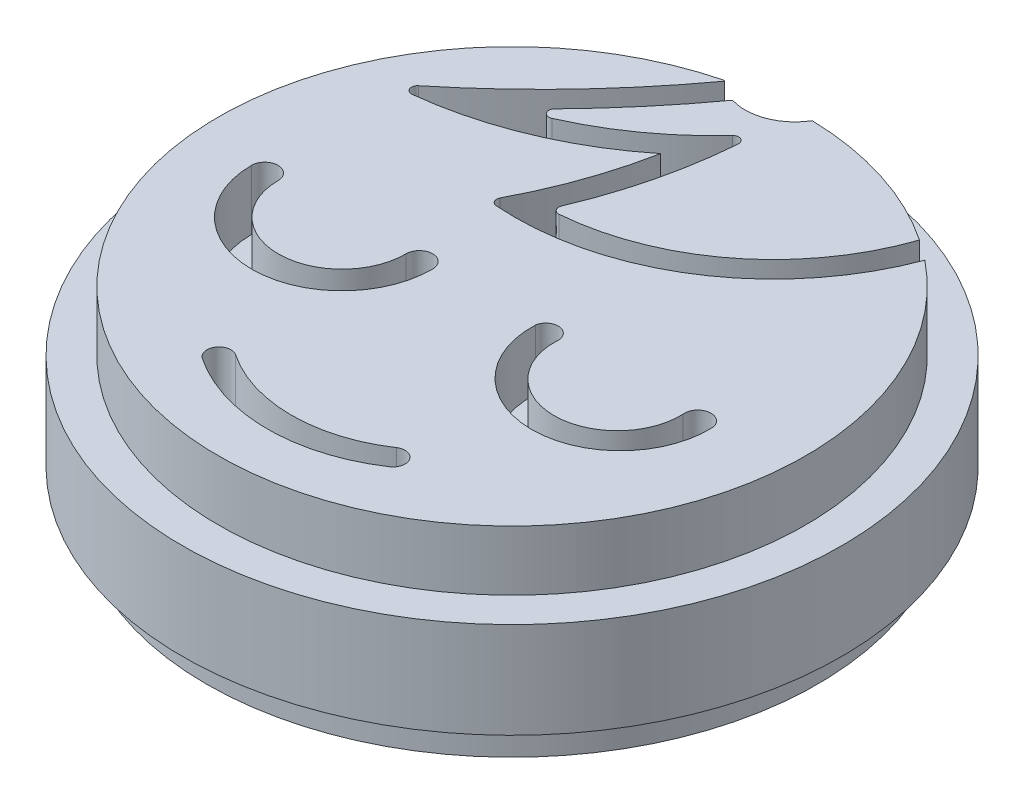
SolidWorks part; units mm, degrees
ref_plane "Alzado" through (0, 0, 0) normal (0, 0, 1) x (1, 0, 0)
ref_plane "Planta" through (0, 0, 0) normal (0, 1, 0) x (1, 0, 0)
ref_plane "Vista lateral" through (0, 0, 0) normal (1, 0, 0) x (0, 0, -1)
sketch "Croquis1" plane through (0, 0, 0) normal (0, 1, 0) x (1, 0, 0)
  line L0 (-8.3007, -65.0348) -> (191.6993, -65.0348) construction
  circle A0 centre (0, 0) radius 27.5
  arc A1 (15.3324, 19.1094) -> (-6.4819, 5.1617) centre (-4.873, 26.678) cw
  arc A2 (-3.3982, 15.7873) -> (-6.8868, 5.8937) centre (-38.63, 22.6486) cw
  arc A3 (-18.0355, 9.7052) -> (-3.3982, 15.7873) centre (-21.2019, 37.9801) ccw
  arc A4 (-18.4064, 10.5902) -> (-5.9012, 23.7787) centre (-62.7407, 65.1506) ccw
  arc A5 (3.7721, -1.8221) -> (18.5666, -1.8221) centre (11.1693, -2.1271) ccw
  arc A6 (16.3721, -2.1271) -> (5.8129, -2.1271) centre (11.0925, -2.3075) cw
  arc A7 (3.7721, -1.8221) -> (5.8129, -2.1271) centre (4.7925, -1.9746) cw
  arc A8 (18.5666, -1.8221) -> (16.3721, -2.1271) centre (17.4693, -1.9746) ccw
  arc A9 (-19.6178, -2.1324) -> (-4.5632, -2.0598) centre (-12.0905, -2.0961) ccw
  arc A10 (-17.4052, -2.1217) -> (-6.7758, -2.0705) centre (-12.0905, -2.0961) ccw
  arc A11 (-19.6178, -2.1324) -> (-17.4052, -2.1217) centre (-18.5115, -2.1271) cw
  arc A12 (-6.7758, -2.0705) -> (-4.5632, -2.0598) centre (-5.6695, -2.0652) cw
  arc A13 (-7.7057, -18.14) -> (7.9339, -18.14) centre (0.1141, -6.4787) ccw
  arc A14 (-6.5918, -16.4789) -> (6.82, -16.4789) centre (0.1141, -6.4787) ccw
  arc A15 (-6.5918, -16.4789) -> (-7.7057, -18.14) centre (-7.1487, -17.3095) ccw
  arc A16 (6.82, -16.4789) -> (7.9339, -18.14) centre (7.3769, -17.3095) cw
  arc A17 (13.6507, 20.3448) -> (-3.2376, 7.17) centre (-4.873, 26.678) cw
  arc A18 (-0.8501, 19.7141) -> (-3.7398, 7.8634) centre (-38.63, 22.6486) cw
  arc A19 (-10.4829, 13.7976) -> (-1.7169, 20.0909) centre (-21.2019, 37.9801) ccw
  arc A20 (-11.043, 14.6043) -> (-4.2484, 22.6509) centre (-62.7407, 65.1506) ccw
  arc A21 (-5.9012, 23.7787) -> (0.5539, 24.4937) centre (0, 0) ccw
  arc A22 (-6.0244, 23.7478) -> (-5.9667, 23.6888) centre (-3.0195, 26.6269) ccw
  arc A23 (15.5115, 19.6059) -> (-7.2448, 5.2323) centre (-4.873, 26.678) cw construction
  arc A24 (13.622, 20.2615) -> (-4.065, 7.1183) centre (-4.873, 26.678) cw construction
  arc A27 (-12.7506, 12.9149) -> (-4.2841, 22.6017) centre (-62.7407, 65.1506) ccw construction
  arc A28 (-4.2484, 22.6509) -> (0.5539, 24.4937) centre (-3.0195, 26.6269) ccw
  arc A29 (-0.7645, 21.1873) -> (-4.065, 7.1183) centre (-38.63, 22.6486) cw construction
  arc A30 (-3.2376, 7.17) -> (-3.7398, 7.8634) centre (-3.2794, 7.6683) cw
  arc A31 (-3.3982, 15.7873) -> (-7.2448, 5.2323) centre (-38.63, 22.6486) cw construction
  arc A32 (-6.4819, 5.1617) -> (-6.8868, 5.8937) centre (-6.4446, 5.6603) cw
  arc A33 (-19.6943, 9.5685) -> (-3.3982, 15.7873) centre (-21.2019, 37.9801) ccw construction
  arc A34 (-19.6943, 9.5685) -> (-5.9012, 23.7787) centre (-62.7407, 65.1506) ccw construction
  arc A35 (-18.0355, 9.7052) -> (-18.4064, 10.5902) centre (-18.0911, 10.2021) cw
  arc A36 (-12.7506, 12.9149) -> (-0.7645, 21.1873) centre (-21.2019, 37.9801) ccw construction
  arc A37 (-10.4829, 13.7976) -> (-11.043, 14.6043) centre (-10.6855, 14.2548) cw
  arc A38 (-0.8501, 19.7141) -> (-1.7169, 20.0909) centre (-1.3486, 19.7528) ccw
  arc A41 (-26.4032, -7.6889) -> (26.3995, -7.7018) centre (0, 0) ccw
  arc A44 (-26.4032, -7.6889) -> (26.3995, -7.7018) centre (0, 0) ccw
  arc A47 (27.167, 4.2668) -> (-27.1691, 4.2535) centre (0, 0) ccw
  point P53 (22, 0)
  point P79 (23.9076, 7.3093)
  dimension "D5" = 0.5
  dimension "D6" = 0.5
  dimension "D2" = 2
  dimension "D3" = 2
extrude "Saliente-Extruir1" add sketch "Croquis1" along normal blind 5 contours A3 A35 A4 A22 A21 A1 A32 A2 A14 A16 A13 A15 A8 A5 A7 A6 A10 A12 A9 A11 | A38 A18 A30 A17 A21 A28 A20 A37 A19
sketch "Croquis2" plane through (0, 0, 0) normal (0, -1, 0) x (-1, 0, 0)
  circle A0 centre (0, 0) radius 27.5
  dimension "D1" = 55
extrude "Saliente-Extruir2" add sketch "Croquis2" along normal blind 8
sketch "Croquis3" plane through (0, -8, 0) normal (0, -1, 0) x (-1, 0, 0)
  circle A0 centre (0, 0) radius 25.5
  circle A1 centre (0, 0) radius 24
  point P4 (0, -25.5)
  point P5 (0, -24)
  dimension "D1" = 51
  dimension "D2" = 48
extrude "Saliente-Extruir3" add sketch "Croquis3" along normal blind 3
sketch "Croquis4" plane through (0, -8, 0) normal (0, -1, 0) x (-1, 0, 0)
  circle A0 centre (0, 0) radius 24
extrude "Cortar-Extruir1" cut sketch "Croquis4" against normal blind 3
